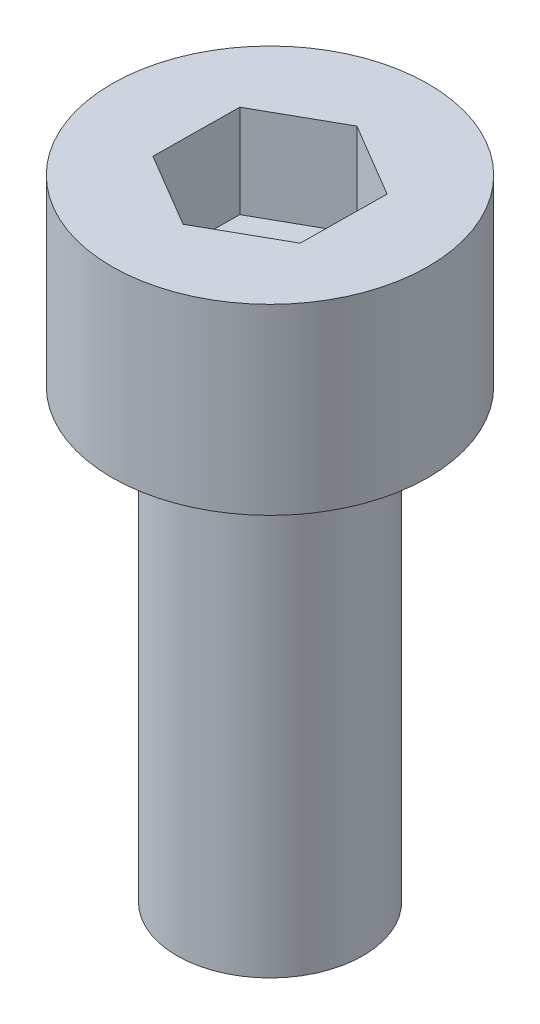
SolidWorks part; units mm, degrees
ref_plane "前视基准面" through (0, 0, 0) normal (0, 0, 1) x (1, 0, 0)
ref_plane "上视基准面" through (0, 0, 0) normal (0, 1, 0) x (1, 0, 0)
ref_plane "右视基准面" through (0, 0, 0) normal (1, 0, 0) x (0, 0, -1)
sketch "草图1" plane through (0, 0, 0) normal (0, 1, 0) x (1, 0, 0)
  circle A0 centre (0, 0) radius 2.5
  dimension "D1" = 5
extrude "凸台-拉伸1" add sketch "草图1" along normal blind 12
sketch "草图2" plane through (0, 12, 0) normal (0, 1, 0) x (1, 0, 0)
  circle A0 centre (0, 0) radius 4.25
  dimension "D1" = 8.5
extrude "凸台-拉伸2" add sketch "草图2" along normal blind 4.91
sketch "草图3" plane through (0, 16.91, 0) normal (0, 1, 0) x (1, 0, 0)
  line L1 (1.9872, -1.1765) -> (2.0125, 1.1327)
  line L2 (2.0125, 1.1327) -> (0.0253, 2.3093)
  line L3 (0.0253, 2.3093) -> (-1.9872, 1.1765)
  line L4 (-1.9872, 1.1765) -> (-2.0125, -1.1327)
  line L5 (-2.0125, -1.1327) -> (-0.0253, -2.3093)
  line L6 (-0.0253, -2.3093) -> (1.9872, -1.1765)
  circle A0 centre (0, 0) radius 2 construction
  dimension "D1" = 4
extrude "切除-拉伸1" cut sketch "草图3" against normal blind 2.5
